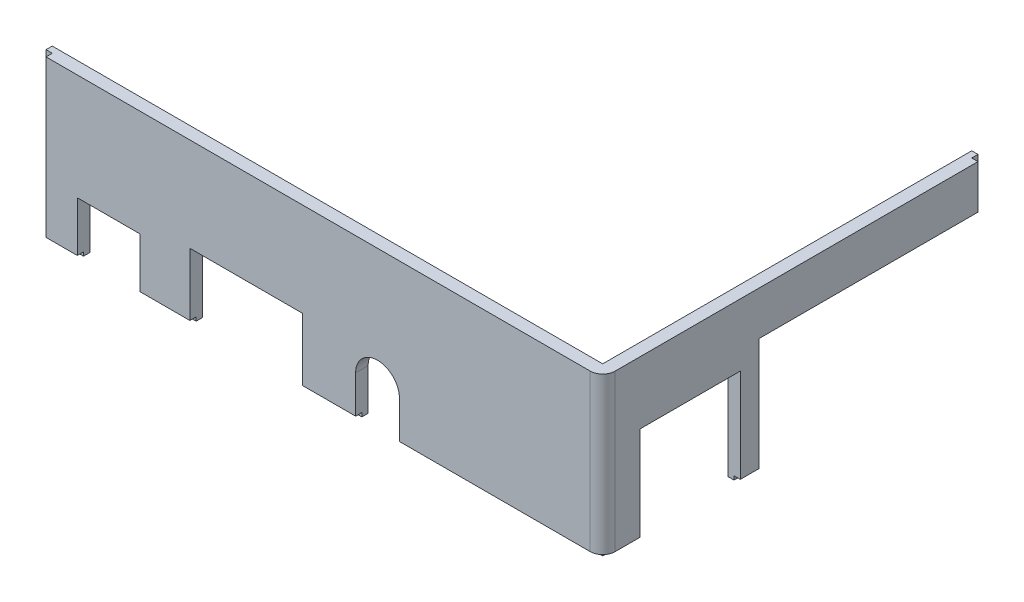
SolidWorks part; units mm, degrees
ref_plane "Přední rovina" through (0, 0, 0) normal (0, 0, 1) x (1, 0, 0)
ref_plane "Horní rovina" through (0, 0, 0) normal (0, 1, 0) x (1, 0, 0)
ref_plane "Pravá rovina" through (0, 0, 0) normal (1, 0, 0) x (0, 0, -1)
sketch "Skica1" plane through (0, 0, 0) normal (0, 1, 0) x (1, 0, 0)
  line L1 (0, 0) -> (90, 0)
  line L2 (0, 0) -> (0, 2)
  line L3 (0, 2) -> (90, 2)
  line L4 (90, 0) -> (90, 2)
  line L9 (90, 2) -> (88, 2)
  line L10 (90, 2) -> (90, 61)
  line L11 (90, 61) -> (88, 61)
  line L12 (88, 2) -> (88, 61)
  line L17 (0, 0) -> (1, 0)
  line L18 (0, 0) -> (0, 1)
  line L19 (0, 1) -> (1, 1)
  line L20 (1, 0) -> (1, 1)
  line L21 (90, 61) -> (89, 61)
  line L22 (90, 61) -> (90, 60)
  line L23 (90, 60) -> (89, 60)
  line L24 (89, 61) -> (89, 60)
  dimension "D1" = 2
  dimension "D2" = 90
  dimension "D3" = 1
  dimension "D4" = 61
  dimension "D5" = 2
  dimension "D6" = 1
extrude "Přidat vysunutím1" add sketch "Skica1" along normal blind 25 contours L24 L11 L12 L3 L10 L23 | L20 L1 L4 L3 L2 L19
sketch "Skica2" plane through (0, 0, 0) normal (0, -1, 0) x (1, 0, 0)
  line L0 (0, -1) -> (0, -2) construction
  line L1 (0, -1) -> (88, -1)
  line L2 (0, -1) -> (0, -2)
  line L3 (0, -2) -> (88, -2)
  line L4 (88, -1) -> (88, -2)
  line L5 (89, -61) -> (88, -61)
  line L6 (89, -61) -> (89, -1)
  line L7 (89, -1) -> (88, -1)
  line L8 (88, -61) -> (88, -1)
  line L9 (0, -1) -> (1, -1) construction
extrude "Přidat vysunutím2" add sketch "Skica2" along normal blind 0.6 contours L4 L3 L2 L1 | L8 L5 L6 L7
sketch "Skica5" plane through (0, 0, 0) normal (0, 0, 1) x (1, 0, 0)
  line L0 (1, 25) -> (1, 0) construction
  line L1 (6, 8) -> (16, 8)
  line L2 (6, 8) -> (6, -0.6)
  line L3 (6, -0.6) -> (16, -0.6)
  line L4 (16, 8) -> (16, -0.6)
  line L5 (11, 8) -> (11, -0.7728) construction
  line L6 (1, 0) -> (89, 0) construction
  line L7 (0, -0.6) -> (0, 25) construction
  line L8 (24, -0.6) -> (42, -0.6)
  line L9 (24, -0.6) -> (24, 10)
  line L10 (24, 10) -> (42, 10)
  line L11 (42, -0.6) -> (42, 10)
  line L13 (0, -0.6) -> (88, -0.6) construction
  line L14 (1, 0) -> (90, 0) construction
  line L15 (0, -0.6) -> (89, -0.6) construction
  line L16 (33, 10) -> (33, -0.6) construction
  line L17 (50.5, 6) -> (50.5, -0.6)
  line L18 (57.5, 6) -> (57.5, -0.6)
  line L19 (50.5, -0.6) -> (57.5, -0.6)
  arc A1 (50.5, 6) -> (57.5, 6) centre (54, 6) cw
  dimension "D7" = 7
  dimension "D9" = 6
  dimension "D1" = 8
  dimension "D2" = 10
  dimension "D3" = 10
  dimension "D4" = 32
  dimension "D5" = 18
  dimension "D6" = 10
  dimension "D8" = 54
extrude "Odebrat vysunutím1" cut sketch "Skica5" against normal up to next
sketch "Skica6" plane through (90, 0, 0) normal (1, 0, 0) x (0, 0, -1)
  line L1 (6, -0.6) -> (22, -0.6)
  line L2 (6, -0.6) -> (6, 15)
  line L3 (6, 15) -> (22, 15)
  line L4 (22, -0.6) -> (22, 15)
  line L9 (42, -0.6) -> (61, -0.6)
  line L10 (42, -0.6) -> (42, 18)
  line L11 (42, 18) -> (61, 18)
  line L12 (61, -0.6) -> (61, 18)
  line L13 (14, 15) -> (14, -0.6) construction
  line L18 (25, -0.6) -> (41, -0.6)
  line L19 (25, -0.6) -> (25, 18)
  line L20 (25, 18) -> (41, 18)
  line L21 (41, -0.6) -> (41, 18)
  line L22 (33, 18) -> (33, -0.6) construction
  line L23 (61, 25) -> (61, -0.6) construction
  line L24 (51.5, 18) -> (51.5, -0.6) construction
  line L25 (60, 25) -> (60, 0) construction
  line L28 (61, -0.6) -> (1, -0.6) construction
  line L29 (0, 0) -> (60, 0) construction
  line L30 (60, 0) -> (1, 0) construction
  dimension "D1" = 18
  dimension "D2" = 27
  dimension "D3" = 46
  dimension "D4" = 16
  dimension "D5" = 15
  dimension "D6" = 16
  dimension "D7" = 18
extrude "Odebrat vysunutím2" cut sketch "Skica6" against normal up to next
fillet "Fillet1" radius 2 1 edges at (90, 12.5, 0)
sketch "Sketch1" plane through (90, 0, 0) normal (1, 0, 0) x (0, 0, -1)
  line L0 (0, 21.5) -> (-0.4, 21.5)
  line L1 (0, 0) -> (0, 25) construction
  line L2 (2, 25) -> (60, 25) construction
  line L3 (0, 22) -> (0, 21)
  arc A0 (0, 22) -> (0, 21) centre (-0.4, 21.5) cw
  dimension "D2" = 1
  dimension "D1" = 0.4
  dimension "D3" = 4
sketch "Sketch2" plane through (90, 0, 0) normal (1, 0, 0) x (0, 0, -1)
  line L1 (41, 18) -> (42, 18)
  line L2 (41, 18) -> (41, -0.6)
  line L3 (41, -0.6) -> (42, -0.6)
  line L4 (42, 18) -> (42, -0.6)
extrude "Cut-Extrude2" cut sketch "Sketch2" against normal up to next
